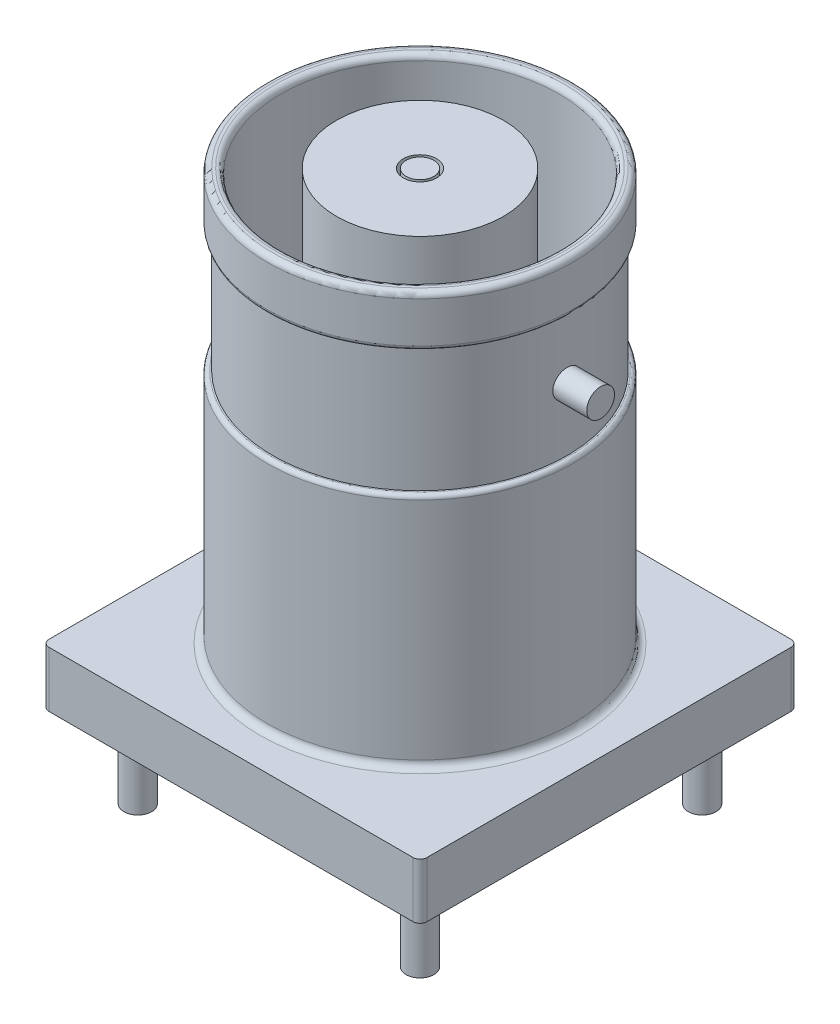
SolidWorks part; units mm, degrees
ref_plane "Front Plane" through (0, 0, 0) normal (0, 0, 1) x (1, 0, 0)
ref_plane "Top Plane" through (0, 0, 0) normal (0, 1, 0) x (1, 0, 0)
ref_plane "Right Plane" through (0, 0, 0) normal (1, 0, 0) x (0, 0, -1)
sketch "Sketch1" plane through (0, 0, 0) normal (0, 1, 0) x (1, 0, 0)
  line L0 (0, 6.8) -> (0, -6.8) construction
  line L1 (-6.8, 0) -> (6.8, 0) construction
  line L2 (6.8, 6.8) -> (-6.8, -6.8) construction
  line L3 (-6.55, -6.8) -> (6.55, -6.8)
  line L4 (-6.8, -6.55) -> (-6.8, 6.55)
  line L5 (-6.55, 6.8) -> (6.55, 6.8)
  line L6 (6.8, -6.55) -> (6.8, 6.55)
  arc A0 (-6.55, 6.8) -> (-6.8, 6.55) centre (-6.55, 6.55) ccw
  arc A1 (-6.8, -6.55) -> (-6.55, -6.8) centre (-6.55, -6.55) ccw
  arc A2 (6.8, -6.55) -> (6.55, -6.8) centre (6.55, -6.55) cw
  arc A3 (6.8, 6.55) -> (6.55, 6.8) centre (6.55, 6.55) ccw
  point P11 (-6.8, 6.8)
  dimension "D2" = 0.25
  dimension "D1" = 13.6
extrude "Base-Extrude" add sketch "Sketch1" along normal blind 2
sketch "Sketch3" plane through (0, 0, 0) normal (1, 0, 0) x (0, 0, -1)
  line L0 (0, 0) -> (0, 10.3168) construction
  line L1 (5.5, 2.25) -> (5.5, 10.35)
  line L2 (6.55, 2) -> (-6.55, 2) construction
  line L3 (5.35, 15) -> (5.3, 15)
  line L4 (5.3, 15) -> (5.3, 10.5)
  line L5 (5.3, 10.5) -> (5.35, 10.5)
  line L6 (5.5, 15.15) -> (5.5, 16.62)
  line L7 (5.3, 16.82) -> (5.2, 16.82)
  line L8 (5, 16.62) -> (5, 2)
  line L9 (5, 2) -> (5.75, 2)
  line L10 (-6.55, 2) -> (6.55, 2) construction
  line L11 (-6.55, 2) -> (6.55, 2) construction
  arc A0 (5, 16.62) -> (5.2, 16.82) centre (5.2, 16.62) cw
  arc A1 (5.3, 16.82) -> (5.5, 16.62) centre (5.3, 16.62) cw
  arc A2 (5.5, 15.15) -> (5.35, 15) centre (5.35, 15.15) cw
  arc A3 (5.35, 10.5) -> (5.5, 10.35) centre (5.35, 10.35) cw
  arc A4 (5.75, 2) -> (5.5, 2.25) centre (5.75, 2.25) cw
  point P15 (5, 16.82)
  point P18 (5.5, 16.82)
  point P23 (5.5, 10.5)
  point P31 (5.5, 2)
  dimension "D7" = 0.2
  dimension "D8" = 0.15
  dimension "D9" = 0.25
  dimension "D1" = 14.82
  dimension "D2" = 0.5
  dimension "D3" = 0.3
  dimension "D4" = 5.5
  dimension "D5" = 8.5
  dimension "D6" = 4.5
revolve "Boss-Revolve1" add sketch "Sketch3" angle 360 about L0
sketch "Sketch4" plane through (0, 2, 0) normal (0, 1, 0) x (-1, 0, 0)
  circle A0 centre (0, 0) radius 0.5
  dimension "D1" = 1
extrude "Boss-Extrude1" add sketch "Sketch4" along normal blind 14.8
sketch "Sketch5" plane through (0, 2, 0) normal (0, 1, 0) x (-1, 0, 0)
  circle A0 centre (0, 0) radius 0.6
  circle A1 centre (0, 0) radius 3
  dimension "D1" = 1.2
  dimension "D2" = 6
extrude "Boss-Extrude2" add sketch "Sketch5" along normal up to surface (14.8 mm away) up to face at (0, 16.8, 0.5)
sketch "Sketch6" plane through (0, 0, 0) normal (0, -1, 0) x (1, 0, 0)
  line L0 (7.4017, 0) -> (-7.1425, 0) construction
  line L1 (0, 7.4737) -> (0, -7.7329) construction
  line L2 (0, 0) -> (5.077, -5.077) construction
  circle A0 centre (0, 0) radius 0.5
  circle A1 centre (5.077, -5.077) radius 0.5
  circle A2 centre (-5.077, -5.077) radius 0.5
  circle A3 centre (5.077, 5.077) radius 0.5
  circle A4 centre (-5.077, 5.077) radius 0.5
  dimension "D1" = 1
  dimension "D2" = 7.18
  dimension "D3" = 45
extrude "Boss-Extrude3" add sketch "Sketch6" along normal blind 3
sketch "Sketch7" plane through (0, 0, 0) normal (0, 0, 1) x (1, 0, 0)
  line L0 (-7.9509, 12.75) -> (20.9509, 12.75) construction
  line L1 (6.5, 12.75) -> (5.1, 12.75)
  line L2 (5.1, 13.25) -> (6.5, 13.25)
  line L3 (5.1, 13.25) -> (5.1, 12.75)
  line L5 (6.5, 13.25) -> (6.5, 12.75)
  line L7 (5.3, 10.5) -> (5.3, 15) construction
  line L8 (-6.55, 2) -> (6.55, 2) construction
  point P13 (6.5, 12.75)
  dimension "D1" = 1.2
  dimension "D2" = 0.5
  dimension "D3" = 0.2
  dimension "D4" = 10.75
revolve "Boss-Revolve2" add sketch "Sketch7" angle 360 about L0
mirror "Mirror1" about plane through (0, 0, 0) normal (1, 0, 0) of "Boss-Revolve2"
ref_plane "Plane1" through (0, -0.5, 0) normal (0, 1, 0) x (-1, 0, 0)
sketch "Component_Outline" plane through (0, -0.5, 0) normal (0, 1, 0) x (-1, 0, 0)
  line L0 (6.55, 6.8) -> (-6.55, 6.8)
  line L1 (6.55, 6.8) -> (-6.55, 6.8) construction
  line L2 (-6.8, 6.55) -> (-6.8, -6.55)
  line L3 (-6.55, -6.8) -> (6.55, -6.8)
  line L4 (6.8, -6.55) -> (6.8, 6.55)
  arc A0 (-6.55, 6.8) -> (-6.8, 6.55) centre (-6.55, 6.55) ccw
  arc A1 (-6.8, -6.55) -> (-6.55, -6.8) centre (-6.55, -6.55) ccw
  arc A2 (6.55, -6.8) -> (6.8, -6.55) centre (6.55, -6.55) ccw
  arc A3 (6.8, 6.55) -> (6.55, 6.8) centre (6.55, 6.55) ccw
  point P20 (0, 0)
